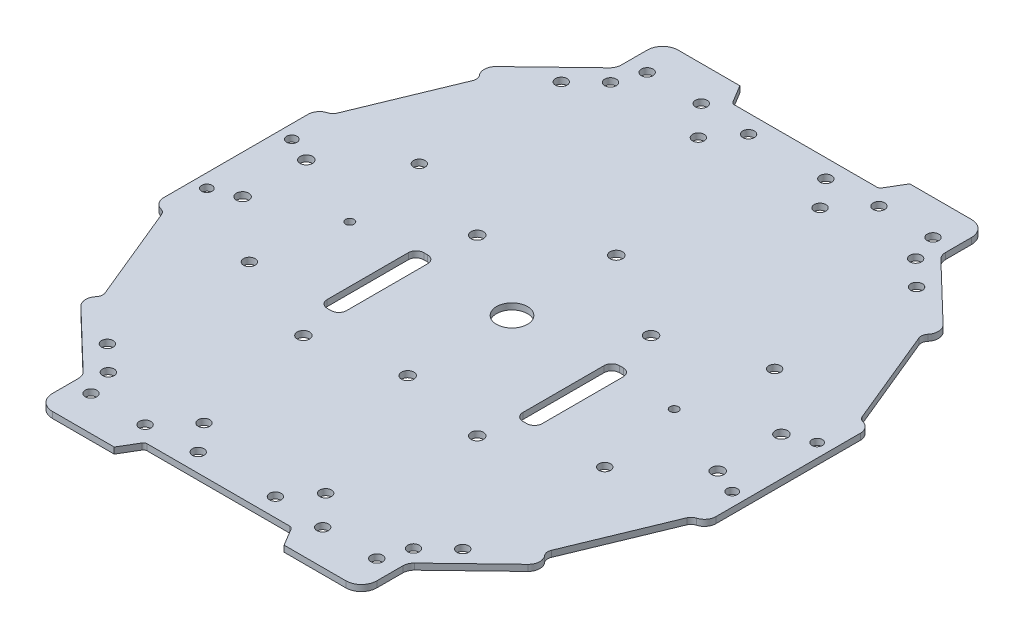
SolidWorks part; units mm, degrees
ref_plane "Front Plane" through (0, 0, 0) normal (0, 0, 1) x (1, 0, 0)
ref_plane "Top Plane" through (0, 0, 0) normal (0, 1, 0) x (1, 0, 0)
ref_plane "Right Plane" through (0, 0, 0) normal (1, 0, 0) x (0, 0, -1)
ref_plane "Plane1"
sketch "Sketch1" plane through (0, 0, 0) normal (0, 1, 0) x (-1, 0, 0)
  line L0 (97.7752, 107.0599) -> (100.7752, 102.0599)
  line L1 (100.7752, 102.0599) -> (120.7752, 102.0599)
  line L2 (120.7752, 102.0599) -> (120.7752, 114.0599)
  line L4 (138.795, 131.3886) -> (136.0224, 134.2718)
  line L5 (136.0224, 134.2718) -> (147.2752, 161.5599)
  line L6 (147.2752, 161.5599) -> (150.2752, 161.5599)
  line L7 (150.2752, 161.5599) -> (150.2752, 183.0599)
  line L8 (150.2752, 183.0599) -> (150.2752, 204.5599)
  line L9 (150.2752, 204.5599) -> (147.2752, 204.5599)
  line L10 (147.2752, 204.5599) -> (136.0224, 231.8479)
  line L11 (136.0224, 231.8479) -> (138.795, 234.7311)
  line L13 (120.7752, 252.0599) -> (120.7752, 264.0599)
  line L14 (120.7752, 264.0599) -> (100.7752, 264.0599)
  line L15 (100.7752, 264.0599) -> (97.7752, 259.0599)
  line L16 (97.7752, 259.0599) -> (78.7752, 259.0599)
  line L17 (78.7752, 259.0599) -> (59.7752, 259.0599)
  line L18 (59.7752, 259.0599) -> (56.7752, 264.0599)
  line L19 (56.7752, 264.0599) -> (36.7752, 264.0599)
  line L20 (36.7752, 264.0599) -> (36.7752, 252.0599)
  line L21 (36.7752, 252.0599) -> (18.7553, 234.7311)
  line L22 (18.7553, 234.7311) -> (21.5279, 231.8479)
  line L23 (21.5279, 231.8479) -> (10.2752, 204.5599)
  line L24 (10.2752, 204.5599) -> (7.2752, 204.5599)
  line L25 (7.2752, 204.5599) -> (7.2752, 183.0599)
  line L26 (7.2752, 183.0599) -> (7.2752, 161.5599)
  line L27 (7.2752, 161.5599) -> (10.2752, 161.5599)
  line L28 (10.2752, 161.5599) -> (21.5279, 134.2718)
  line L29 (21.5279, 134.2718) -> (18.7553, 131.3886)
  line L30 (18.7553, 131.3886) -> (36.7752, 114.0599)
  line L31 (36.7752, 114.0599) -> (36.7752, 102.0599)
  line L32 (36.7752, 102.0599) -> (56.7752, 102.0599)
  line L33 (56.7752, 102.0599) -> (59.7752, 107.0599)
  line L34 (59.7752, 107.0599) -> (78.7752, 107.0599)
  line L35 (78.7752, 107.0599) -> (97.7752, 107.0599)
  line L36 (120.7752, 252.0599) -> (138.795, 234.7311)
  line L37 (138.795, 131.3886) -> (120.7752, 114.0599)
  line L39 (53.6123, 205.4008) -> (52.6123, 205.4008)
  line L40 (55.6123, 203.4008) -> (55.6123, 182.4008)
  line L41 (53.6123, 180.4008) -> (52.6123, 180.4008)
  line L42 (33.0963, 144.5594) -> (33.8666, 148.2549)
  line L43 (34.3058, 148.8139) -> (36.9931, 150.0936)
  line L44 (50.6123, 203.4008) -> (50.6123, 182.4008)
  line L45 (103.2752, 205.4008) -> (104.2752, 205.4008)
  line L46 (101.2752, 203.4008) -> (101.2752, 182.4008)
  line L47 (103.2752, 180.4008) -> (104.2752, 180.4008)
  line L48 (106.2752, 203.4008) -> (106.2752, 182.4008)
  circle A0 centre (78.7752, 183.0599) radius 4
  circle A1 centre (41.7752, 111.0599) radius 1.5
  circle A2 centre (68.7752, 111.8099) radius 1.5
  arc A3 (101.2752, 182.4008) -> (103.2752, 180.4008) centre (103.2752, 182.4008) ccw
  circle A4 centre (101.2752, 169.5599) radius 1.6
  circle A5 centre (56.2752, 169.5599) radius 1.6
  arc A6 (106.2752, 182.4008) -> (104.2752, 180.4008) centre (104.2752, 182.4008) cw
  arc A7 (104.2752, 205.4008) -> (106.2752, 203.4008) centre (104.2752, 203.4008) cw
  arc A8 (33.0963, 144.5594) -> (33.474, 143.2865) centre (34.4668, 144.2736) ccw
  arc A9 (34.3058, 148.8139) -> (33.8666, 148.2549) centre (34.6498, 148.0916) ccw
  arc A10 (38.0183, 150.0518) -> (36.9931, 150.0936) centre (37.4661, 149.1004) ccw
  arc A11 (38.0183, 150.0518) -> (38.6908, 150.0352) centre (38.3697, 150.6572) ccw
  arc A12 (103.2752, 205.4008) -> (101.2752, 203.4008) centre (103.2752, 203.4008) ccw
  arc A13 (53.6123, 205.4008) -> (55.6123, 203.4008) centre (53.6123, 203.4008) cw
  arc A14 (52.6123, 205.4008) -> (50.6123, 203.4008) centre (52.6123, 203.4008) ccw
  arc A15 (52.6123, 180.4008) -> (50.6123, 182.4008) centre (52.6123, 182.4008) cw
  arc A16 (53.6123, 180.4008) -> (55.6123, 182.4008) centre (53.6123, 182.4008) ccw
  circle A20 centre (10.7752, 172.0599) radius 1.35
  circle A21 centre (68.7752, 254.3099) radius 1.5
  circle A23 centre (55.7752, 255.0599) radius 1.5
  circle A24 centre (32.7752, 205.0599) radius 1.5
  circle A25 centre (17.2752, 191.3099) radius 1.6
  circle A26 centre (94.5252, 119.0599) radius 1.5
  circle A37 centre (101.7752, 111.0599) radius 1.5
  circle A38 centre (124.7752, 161.0599) radius 1.5
  circle A39 centre (146.7752, 172.0599) radius 1.35
  circle A40 centre (118.2752, 248.0599) radius 1.5
  circle A41 centre (101.7752, 255.0599) radius 1.5
  circle A58 centre (94.5252, 247.0599) radius 1.5
  circle A60 centre (124.7752, 205.0599) radius 1.5
  circle A61 centre (146.7752, 194.0599) radius 1.35
  circle A62 centre (140.2752, 191.3099) radius 1.6
  circle A63 centre (88.7752, 254.3099) radius 1.5
  circle A64 centre (115.7752, 255.0599) radius 1.5
  circle A65 centre (140.2752, 174.8099) radius 1.6
  circle A66 centre (118.2752, 118.0599) radius 1.5
  circle A67 centre (115.7752, 111.0599) radius 1.5
  circle A69 centre (88.7752, 111.8099) radius 1.5
  circle A70 centre (10.7752, 194.0599) radius 1.35
  circle A71 centre (39.2752, 248.0599) radius 1.5
  circle A72 centre (41.7752, 255.0599) radius 1.5
  circle A73 centre (63.0252, 247.0599) radius 1.5
  circle A90 centre (17.2752, 174.8099) radius 1.6
  circle A91 centre (32.7752, 161.0599) radius 1.5
  circle A92 centre (63.0252, 119.0599) radius 1.5
  circle A93 centre (39.2752, 118.0599) radius 1.5
  circle A94 centre (55.7752, 111.0599) radius 1.5
  circle A95 centre (32.7752, 124.3099) radius 1.5
  arc A97 (78.7752, 154.4599) -> (78.7752, 157.6599) centre (78.7752, 156.0599) ccw
  arc A98 (78.7752, 157.6599) -> (78.7752, 154.4599) centre (78.7752, 156.0599) ccw
  circle A99 centre (56.2752, 214.5599) radius 1.6
  circle A100 centre (32.7752, 241.8099) radius 1.5
  circle A114 centre (124.7752, 124.3099) radius 1.5
  arc A142 (35.6792, 183.0599) -> (37.8711, 183.0599) centre (36.7752, 183.0599) ccw
  arc A143 (37.8711, 183.0599) -> (35.6792, 183.0599) centre (36.7752, 183.0599) ccw
  circle A144 centre (124.7752, 241.8099) radius 1.5
  arc A145 (78.7752, 208.4599) -> (78.7752, 211.6599) centre (78.7752, 210.0599) ccw
  arc A146 (78.7752, 211.6599) -> (78.7752, 208.4599) centre (78.7752, 210.0599) ccw
  arc A147 (121.8711, 183.0599) -> (119.6792, 183.0599) centre (120.7752, 183.0599) ccw
  arc A148 (119.6792, 183.0599) -> (121.8711, 183.0599) centre (120.7752, 183.0599) ccw
  circle A160 centre (101.2752, 214.5599) radius 1.6
  dimension "D1" = 162
  dimension "D2" = 31.5
  dimension "D6" = 2
  dimension "D3" = 45
  dimension "D4" = 45
  dimension "D5" = 22.5
extrude "Extrusion1" add sketch "Sketch1" along normal blind 1.6
fillet "Fillet1" radius 1 4 edges at (-97.7752, 0.8, 107.0599) (-59.7752, 0.8, 107.0599) (-59.7752, 0.8, 259.0599) (-97.7752, 0.8, 259.0599)
fillet "Fillet2" radius 4 4 edges at (-120.7752, 0.8, 102.0599) (-36.7752, 0.8, 102.0599) (-120.7752, 0.8, 264.0599) (-36.7752, 0.8, 264.0599)
fillet "Fillet3" radius 3 4 edges at (-120.7752, 0.8, 114.0599) (-36.7752, 0.8, 114.0599) (-36.7752, 0.8, 252.0599) (-120.7752, 0.8, 252.0599)
fillet "Fillet4" radius 3 1 edges at (-138.795, 0.8, 234.7311)
fillet "Fillet5" radius 2 1 edges at (-136.0224, 0.8, 231.8479)
fillet "Fillet6" radius 2 1 edges at (-21.5279, 0.8, 231.8479)
fillet "Fillet7" radius 3 1 edges at (-18.7553, 0.8, 234.7311)
fillet "Fillet8" radius 3 2 edges at (-138.795, 0.8, 131.3886) (-18.7553, 0.8, 131.3886)
fillet "Fillet9" radius 2 2 edges at (-21.5279, 0.8, 134.2718) (-136.0224, 0.8, 134.2718)
fillet "Fillet10" radius 2 4 edges at (-10.2752, 0.8, 161.5599) (-10.2752, 0.8, 204.5599) (-147.2752, 0.8, 204.5599) (-147.2752, 0.8, 161.5599)
fillet "Fillet11" radius 3 4 edges at (-150.2752, 0.8, 161.5599) (-150.2752, 0.8, 204.5599) (-7.2752, 0.8, 204.5599) (-7.2752, 0.8, 161.5599)
